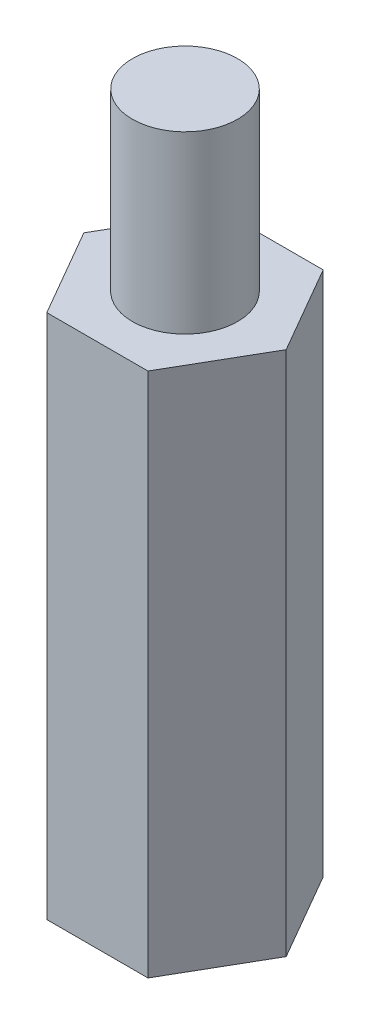
SolidWorks part; units mm, degrees
ref_plane "Front" through (0, 0, 0) normal (0, 0, 1) x (1, 0, 0)
ref_plane "Top" through (0, 0, 0) normal (0, 1, 0) x (1, 0, 0)
ref_plane "Right" through (0, 0, 0) normal (1, 0, 0) x (0, 0, -1)
sketch "草圖1" plane through (0, 0, 0) normal (0, 1, 0) x (1, 0, 0)
  line L1 (2.8868, 0) -> (1.4434, 2.5)
  line L2 (1.4434, 2.5) -> (-1.4434, 2.5)
  line L3 (-1.4434, 2.5) -> (-2.8868, 0)
  line L4 (-2.8868, 0) -> (-1.4434, -2.5)
  line L5 (-1.4434, -2.5) -> (1.4434, -2.5)
  line L6 (1.4434, -2.5) -> (2.8868, 0)
  circle A0 centre (0, 0) radius 2.5 construction
  dimension "D1" = 5
extrude "填料-伸長1" add sketch "草圖1" along normal blind 15
sketch "草圖2" plane through (0, 15, 0) normal (0, 1, 0) x (1, 0, 0)
  circle A0 centre (0, 0) radius 1.5
  dimension "D1" = 3
extrude "填料-伸長2" add sketch "草圖2" along normal blind 5
sketch "草圖3" plane through (0, 0, 0) normal (0, -1, 0) x (1, 0, 0)
  circle A0 centre (0, 0) radius 1.5
  dimension "D1" = 3
extrude "除料-伸長1" cut sketch "草圖3" against normal blind 5
